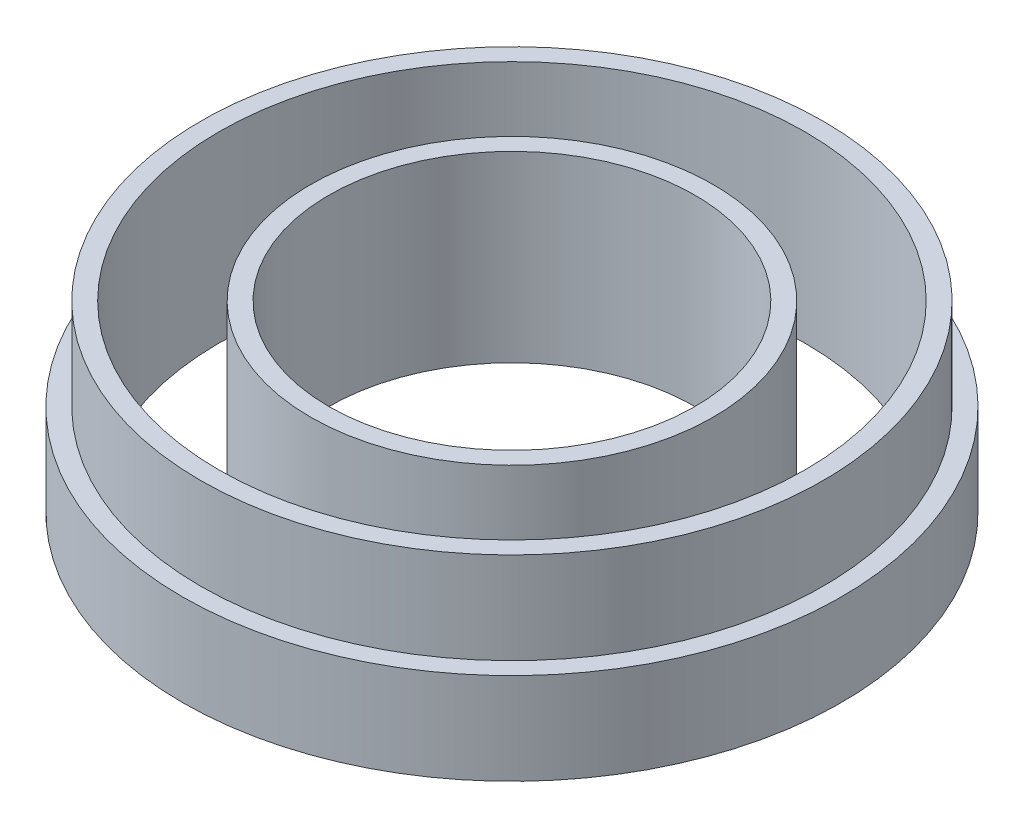
SolidWorks part; units mm, degrees
ref_plane "Front Plane" through (0, 0, 0) normal (0, 0, 1) x (1, 0, 0)
ref_plane "Top Plane" through (0, 0, 0) normal (0, 1, 0) x (1, 0, 0)
ref_plane "Right Plane" through (0, 0, 0) normal (1, 0, 0) x (0, 0, -1)
sketch "Sketch1" plane through (0, 0, 0) normal (0, 1, 0) x (1, 0, 0)
  circle A0 centre (0, 0) radius 5
  circle A1 centre (0, 0) radius 8
  circle A3 centre (0, 0) radius 5.5
  circle A4 centre (0, 0) radius 8.5
  circle A5 centre (0, 6.75) radius 1.25
  point P8 (0, 0)
  dimension "D1" = 10
  dimension "D2" = 16
  dimension "D3" = 11
  dimension "D4" = 17
  dimension "D5" = 2.5
  dimension "D6" = 6.75
extrude "Boss-Extrude1" add sketch "Sketch1" along normal blind 5 contours A3 A0 | A4 A1
sketch "Sketch2" plane through (0, 0, 0) normal (0, 1, 0) x (1, 0, 0)
  circle A0 centre (0, 0) radius 9
  circle A1 centre (0, 0) radius 8.5
  dimension "D1" = 18
  dimension "D2" = 17
extrude "Boss-Extrude3" add sketch "Sketch2" along normal blind 2.5
